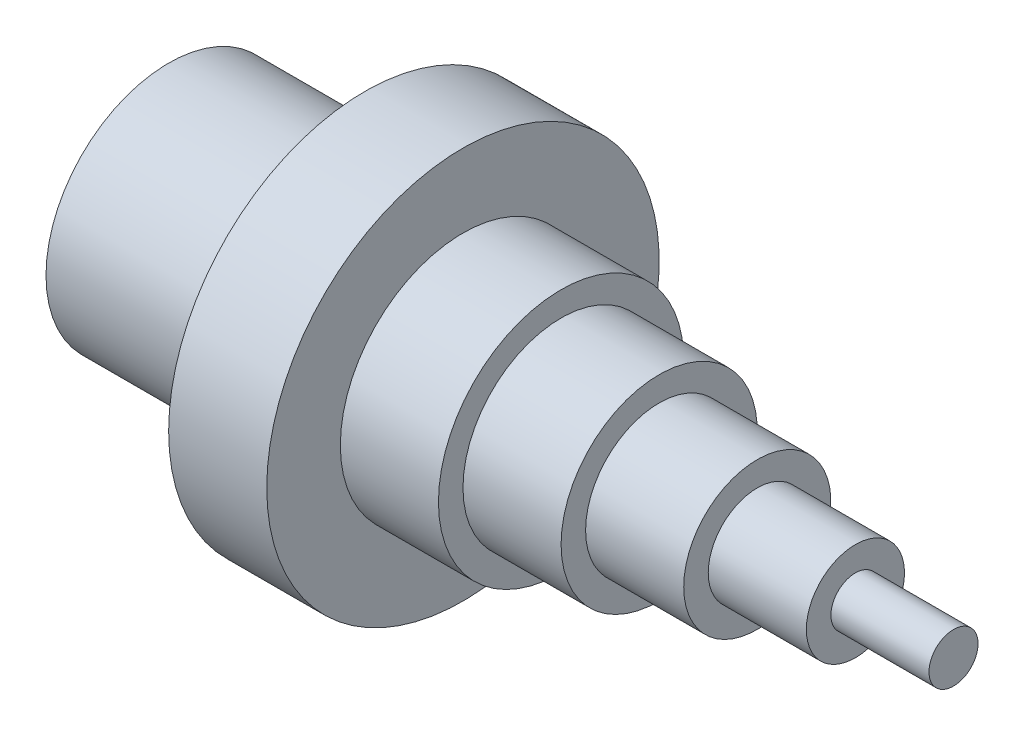
SolidWorks part; units mm, degrees
ref_plane "Front Plane" through (0, 0, 0) normal (0, 0, 1) x (1, 0, 0)
ref_plane "Top Plane" through (0, 0, 0) normal (0, 1, 0) x (1, 0, 0)
ref_plane "Right Plane" through (0, 0, 0) normal (1, 0, 0) x (0, 0, -1)
sketch "Sketch1" plane through (0, 0, 0) normal (0, 0, 1) x (1, 0, 0)
  line L0 (0, 0) -> (161.9577, 0) construction
  line L1 (0, 0) -> (0, 25)
  line L2 (0, 25) -> (40, 25)
  line L3 (40, 25) -> (40, 40)
  line L4 (40, 40) -> (60, 40)
  line L5 (60, 40) -> (60, 25)
  line L6 (60, 25) -> (80, 25)
  line L7 (80, 25) -> (80, 20)
  line L8 (80, 20) -> (100, 20)
  line L9 (100, 20) -> (100, 15)
  line L10 (100, 15) -> (120, 15)
  line L11 (120, 15) -> (120, 10)
  line L12 (120, 10) -> (140, 10)
  line L13 (140, 10) -> (140, 5)
  line L14 (140, 5) -> (160, 5)
  line L15 (160, 5) -> (160, 0)
  line L16 (0, 0) -> (160, 0)
revolve "Revolve1" add sketch "Sketch1" angle 360 about L0
